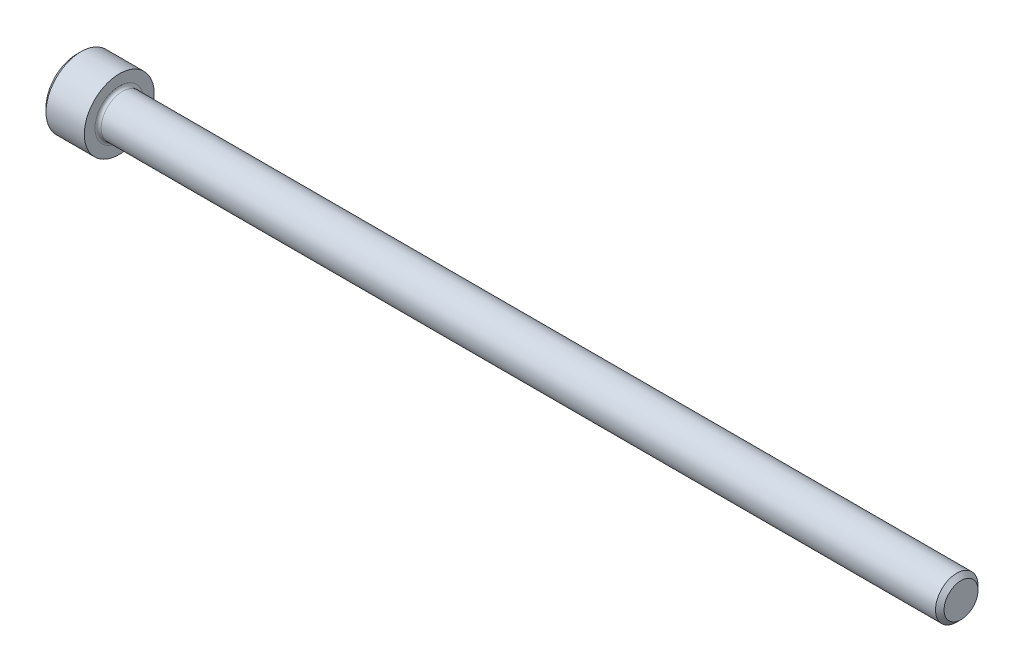
SolidWorks part; units mm, degrees
revolve "Base-Revolve" add sketch "BodySke"
sketch "BodySke" plane through (0, 0, 0) normal (0, 0, 1) x (1, 0, 0)
  line L0 (0, 0) -> (0, 3.0226)
  line L1 (0.4064, 3.429) -> (4.1656, 3.429)
  line L2 (4.1656, 3.429) -> (4.1656, 2.0828)
  line L3 (4.1656, 2.0828) -> (86.2952, 2.0828)
  line L4 (86.7156, 1.6624) -> (86.7156, 0)
  line L5 (86.7156, 0) -> (0, 0)
  line L6 (-31.75, 0) -> (127, 0) construction
  line L7 (0, 3.0226) -> (0.4064, 3.429)
  line L8 (86.7156, 1.6624) -> (86.2952, 2.0828)
  line L9 (0, -3.0226) -> (0.4064, -3.429) construction
  line L10 (86.7156, -1.6624) -> (86.2952, -2.0828) construction
  line L11 (4.8717, 9.525) -> (4.8717, 3.175) construction
  line L12 (64.4906, 9.525) -> (64.4906, 3.175) construction
  line L13 (48.6156, 9.525) -> (48.6156, 3.175) construction
  dimension "Diameter" = 4.1656
  dimension "Head_ht" = 4.1656
  dimension "Length" = 82.55
  dimension "Body_ch_ang" = 45
  dimension "Head_dia" = 6.858
  dimension "Head_ch_ang" = 45
  dimension "Head_side_ht" = 3.7592
  dimension "Minor_dia" = 3.3249
  dimension "Advance" = 0.7061
  dimension "Thread_nom" = 22.225
  dimension "Thread_length" = 38.1
cosmetic thread "ThreadCosmetic" [suppressed]
fillet "Fillet1" radius 0.3048 1 edges at (4.1656, 0, 2.0828)
ref_plane "Plane1" through (0, 0, 0) normal (0, 0, 1) x (1, 0, 0)
ref_plane "Plane2" through (0, 0, 0) normal (0, 1, 0) x (1, 0, 0)
ref_plane "Plane3" through (0, 0, 0) normal (1, 0, 0) x (0, 0, -1)
sketch "Sketch2" plane through (0, 0, 0) normal (0, 0, 1) x (1, 0, 0)
  line L0 (0, 1.778) -> (1.9558, 1.778)
  line L1 (1.9558, 1.778) -> (2.9823, 0)
  line L2 (-31.75, 0) -> (127, 0) construction
  line L3 (2.9823, 0) -> (0, 0)
  line L4 (0, 0) -> (0, 1.778)
  line L5 (0, 3.0226) -> (0, -3.0226) construction
  line L6 (0, 0) -> (47.625, 0) construction
  line L7 (4.1656, -3.429) -> (4.1656, 3.429) construction
  dimension "D2" = 60
revolve "Hex-PreBroach" cut sketch "Sketch2" angle 360 about L6
sketch "Sketch3" plane through (0, 0, 0) normal (-1, 0, 0) x (0, 0.5, 0.866)
  line L0 (1.0265, 1.778) -> (-1.0265, 1.778)
  line L1 (-1.0265, 1.778) -> (-2.0531, 0)
  line L2 (1.0265, 1.778) -> (2.0531, 0)
  line L3 (1.0265, -1.778) -> (2.0531, 0)
  line L4 (1.0265, -1.778) -> (-1.0265, -1.778)
  line L5 (-1.0265, -1.778) -> (-2.0531, 0)
extrude "Hex" cut sketch "Sketch3" against normal blind 1.9558
sketch "Sketch4" plane through (0, 0, 0) normal (-1, 0, 0) x (0, 0, 1)
  line L0 (0, 0) -> (2.1971, 0)
  line L1 (0, 0) -> (6.1484, 3.5498) construction
  line L2 (0, 0) -> (1.0985, 1.9027)
  line L3 (1.8302, 0.5287) -> (2.0897, 0.6786)
  line L4 (1.373, 1.3206) -> (1.6325, 1.4704)
  arc A0 (1.8302, 0.5287) -> (1.373, 1.3206) centre (0, 0) ccw
  arc A1 (2.1971, 0) -> (2.0897, 0.6786) centre (0, 0) ccw
  arc A2 (1.0985, 1.9027) -> (1.6325, 1.4704) centre (0, 0) cw
  dimension "D1" = 30
  dimension "D2" = 60
  dimension "D3" = 0.4572
extrude "Spline" [suppressed] cut sketch "Sketch4" against normal blind 1.9558
pattern_circular "CirPattern1" [suppressed] count 6 every 60
sketch "Sketch5" plane through (0, 0, 0) normal (0, 0, 1) x (1, 0, 0)
  line L0 (-31.75, 0) -> (127, 0) construction
  line L2 (0, 3.0226) -> (0, -3.0226) construction
  circle A0 centre (1.524, 0) radius 0.5905
  dimension "Drilled_hole_dia" = 1.1811
  dimension "Drilled_hole_loc" = 1.524
extrude "Hole" [suppressed] cut sketch "Sketch5" against normal through all and the other way through all
pattern_circular "Drilled-4" [suppressed] count 2 every 60
pattern_circular "Drilled-6" [suppressed] count 3 every 60
sketch "ThdSchSke" plane through (0, 0, 0) normal (0, 0, 1) x (1, 0, 0)
  line L0 (64.4906, -1.6624) -> (64.1963, -2.0828)
  line L1 (64.4906, -1.6624) -> (64.7849, -2.0828)
  line L2 (64.7849, -2.0828) -> (64.7849, -2.6035)
  line L3 (-3.175, 0) -> (5.1513, 0) construction
  line L5 (64.7849, -2.6035) -> (64.1963, -2.6035)
  line L6 (64.1963, -2.6035) -> (64.1963, -2.0828)
  line L7 (0, 3.0226) -> (0, -3.0226) construction
revolve "ThreadSchematic" [suppressed] cut sketch "ThdSchSke" angle 360 about L3
pattern_linear "ThdSchPat" [suppressed]
equation "\"D2@Sketch3\" = \"Hex_size@Sketch3\" / 2"
equation "\"D1@Sketch3\" = \"Hex_size@Sketch3\" / 2"
equation "\"D1@Sketch2\" = \"Hex_size@Sketch3\" / 2"
equation "\"D3@Sketch4\" = \"Spline_p_dim@Sketch4\" / 2"
equation "\"Thread_minor@ThreadCosmetic\"  =  \"Minor_dia@BodySke\""
equation "\"D2@CirPattern1\" = 360 / \"Num_teeth@CirPattern1\""
equation "\"Wall_thickness@Sketch2\" = \"Head_ht@BodySke\" - \"Key_eng@Hex\""
equation "\"Thread_length@ThreadCosmetic\" = ((sgn( (\"Length@BodySke\" - \"Advance@BodySke\" ) - \"Thread_nom@BodySke\" )-1)*( (\"Length@BodySke\" - \"Advance@BodySke\" ) - \"Thread_nom@BodySke\" ))/-2+ \"Thread_nom@BodySke\""
equation "\"Thread_minor@ThdSchSke\" = \"Minor_dia@BodySke\""
equation "\"Diameter@ThdSchSke\" = \"Diameter@BodySke\""
equation "\"Overcut@ThdSchSke\" = \"Diameter@BodySke\" * 1.25"
equation "\"Start@ThdSchSke\" = \"Head_ht@BodySke\" + \"Length@BodySke\" - \"Thread_length@ThreadCosmetic\"  '---Non-countersunk---"
equation "\"Num_threads@ThdSchPat\" = int( \"Thread_length@ThreadCosmetic\" / \"Advance@BodySke\" + 0.999 )  + 1"
equation "\"Advance@ThdSchPat\" = \"Thread_length@ThreadCosmetic\" /  (\"Num_threads@ThdSchPat\" - 1) 'relax it"
equation "\"Num_threads@ThdSchPat\" = \"Num_threads@ThdSchPat\" - sgn( \"Num_threads@ThdSchPat\" - 1) '---chamfered tips only---"
